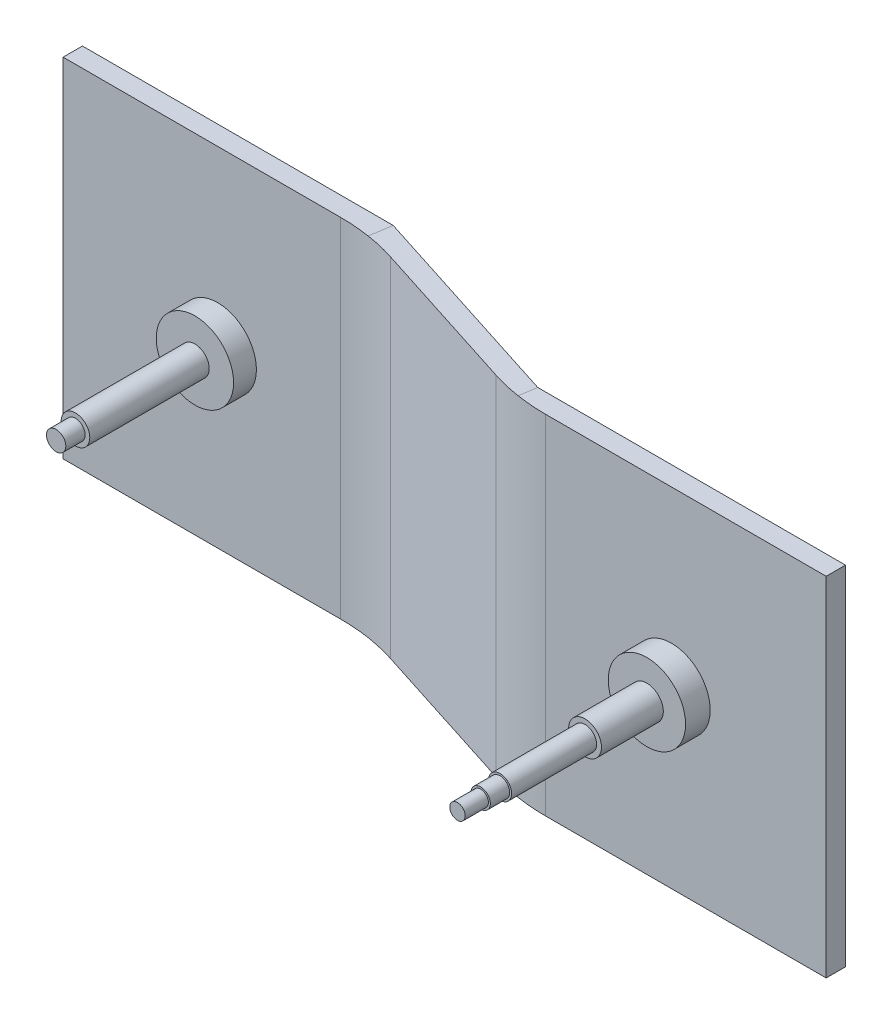
SolidWorks part; units mm, degrees
ref_plane "Piano frontale" through (0, 0, 0) normal (0, 0, 1) x (1, 0, 0)
ref_plane "Piano superiore" through (0, 0, 0) normal (0, 1, 0) x (1, 0, 0)
ref_plane "Piano destro" through (0, 0, 0) normal (1, 0, 0) x (0, 0, -1)
sketch "Schizzo15" plane through (0, 0, 0) normal (0, 1, 0) x (1, 0, 0)
  line L0 (-270, 0) -> (-270, 35.2019) construction
  line L1 (-350, 35.2019) -> (-190, 35.2019)
  line L2 (-190, 35.2019) -> (-80, 0)
  line L4 (-80, 0) -> (80, 0)
  point P4 (-270, 35.2019)
  dimension "D1" = 35.2019
  dimension "D2" = 80
  dimension "D3" = 270
sketch "Schizzo16" plane through (0, 0, 0) normal (1, 0, 0) x (0, 0, -1)
  line L1 (-5, 90) -> (5, 90)
  line L2 (-5, 90) -> (-5, -90)
  line L3 (-5, -90) -> (5, -90)
  line L4 (5, 90) -> (5, -90)
  point P4 (0, 90)
  point P6 (-5, 0)
  dimension "D1" = 10
  dimension "D2" = 180
sweep "Sweep1" add profiles "Schizzo16" path "Schizzo15"
sketch "Schizzo17" plane through (0, 0, 5) normal (0, 0, 1) x (1, 0, 0)
  circle A0 centre (0, 0) radius 20
  dimension "D1" = 40
extrude "Estrusione-Estrusione10" add sketch "Schizzo17" along normal blind 12.7557
sketch "Schizzo18" plane through (0, 0, 17.7557) normal (0, 0, 1) x (1, 0, 0)
  circle A0 centre (0, 0) radius 8.5
  dimension "D1" = 17
extrude "Estrusione-Estrusione11" add sketch "Schizzo18" along normal blind 32
sketch "Schizzo19" plane through (0, 0, 49.7557) normal (0, 0, 1) x (1, 0, 0)
  circle A0 centre (0, 0) radius 6
  dimension "D1" = 12
extrude "Estrusione-Estrusione12" add sketch "Schizzo19" along normal blind 44
sketch "Schizzo20" plane through (0, 0, 93.7557) normal (0, 0, 1) x (1, 0, 0)
  circle A0 centre (0, 0) radius 5
  dimension "D1" = 10
extrude "Estrusione-Estrusione13" add sketch "Schizzo20" along normal blind 10
sketch "Schizzo21" plane through (0, 0, 103.7557) normal (0, 0, 1) x (1, 0, 0)
  circle A0 centre (0, 0) radius 4
  dimension "D1" = 8
extrude "Estrusione-Estrusione14" add sketch "Schizzo21" along normal blind 12
sketch "Schizzo22" plane through (0, 0, -30.2019) normal (0, 0, 1) x (1, 0, 0)
  circle A0 centre (-270, 0) radius 20
  dimension "D1" = 40
extrude "Estrusione-Estrusione15" add sketch "Schizzo22" along normal blind 11.8055
sketch "Schizzo23" plane through (0, 0, -18.3965) normal (0, 0, 1) x (1, 0, 0)
  circle A0 centre (-270, 0) radius 7.4
  dimension "D1" = 14.8
extrude "Estrusione-Estrusione16" add sketch "Schizzo23" along normal blind 61.8
sketch "Schizzo24" plane through (0, 0, 43.4035) normal (0, 0, 1) x (1, 0, 0)
  circle A0 centre (-270, 0) radius 5
  dimension "D1" = 10
extrude "Estrusione-Estrusione17" add sketch "Schizzo24" along normal blind 10
fillet "Raccordo1" radius 100 2 edges at (-80.7805, 0, 5) (-190.7805, 0, -30.2019)
ref_plane "Piano1" through (0, 0, 25) normal (0, 0, 1) x (1, 0, 0)
sketch "Schizzo25" plane through (0, 0, 25) normal (0, 0, 1) x (1, 0, 0)
  line L0 (0, 72.5) -> (-270, 72.5)
  line L1 (0, 80) -> (-270, 80)
  line L2 (0, -72.5) -> (-270, -72.5)
  line L3 (0, -80) -> (-270, -80)
  arc A0 (0, -72.5) -> (0, 72.5) centre (0, 0) ccw
  arc A1 (0, -80) -> (0, 80) centre (0, 0) ccw
  arc A2 (-270, 80) -> (-270, -80) centre (-270, 0) ccw
  arc A3 (-270, 72.5) -> (-270, -72.5) centre (-270, 0) ccw
  dimension "D1" = 145
  dimension "D2" = 145
